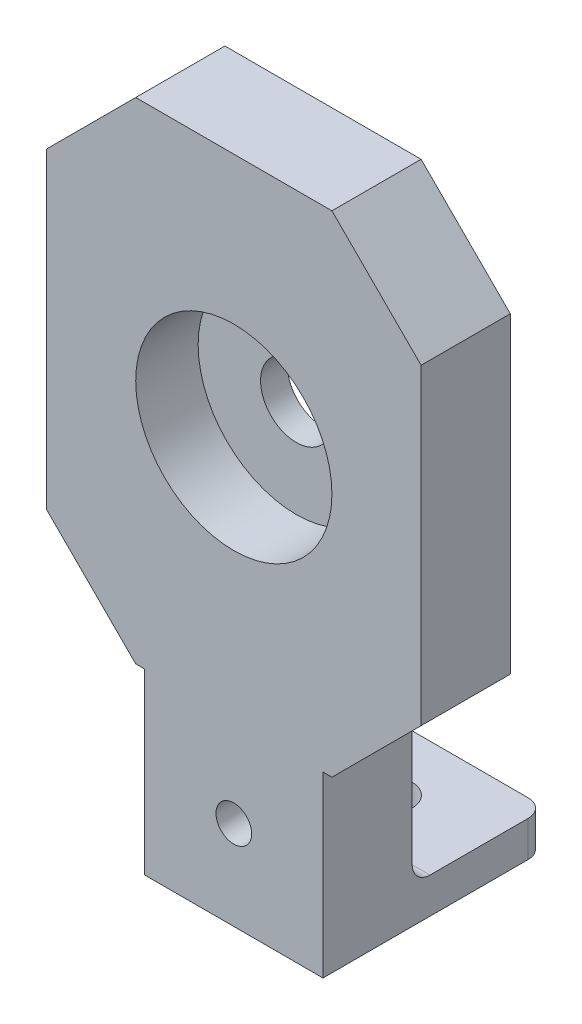
SolidWorks part; units mm, degrees
material "PLA"
ref_plane "Piano frontale" through (0, 0, 0) normal (0, 0, 1) x (1, 0, 0)
ref_plane "Piano superiore" through (0, 0, 0) normal (0, 1, 0) x (1, 0, 0)
ref_plane "Piano destro" through (0, 0, 0) normal (1, 0, 0) x (0, 0, -1)
sketch "Schizzo1" plane through (0, 0, 0) normal (0, 0, 1) x (1, 0, 0)
  line L0 (0, 0) -> (0, -47.5) construction
  line L1 (-10, -47.5) -> (10, -47.5)
  line L2 (-21, -27.5) -> (-21, 27.5)
  line L3 (-21, 27.5) -> (21, 27.5)
  line L4 (21, -27.5) -> (21, 27.5)
  line L5 (-21, -27.5) -> (21, 27.5) construction
  line L6 (-21, 27.5) -> (21, -27.5) construction
  line L7 (-10, -47.5) -> (-10, -27.5)
  line L8 (-10, -27.5) -> (-21, -27.5)
  line L9 (10, -47.5) -> (10, -27.5)
  line L10 (10, -27.5) -> (21, -27.5)
  point P0 (0, 0)
  dimension "D1" = 42
  dimension "D3" = 20
  dimension "D4" = 10
  dimension "D5" = 55
extrude "Estrusione-Estrusione1" add sketch "Schizzo1" along normal blind 10
sketch "Schizzo6" plane through (0, 0, 10) normal (0, 0, 1) x (1, 0, 0)
  line L0 (-10, -47.5) -> (10, -47.5) construction
  line L1 (21, 27.5) -> (-21, 27.5) construction
  circle A0 centre (0, 0) radius 11
  dimension "D1" = 22
  dimension "D2" = 47.5
extrude "Taglio-Estrusione4" cut sketch "Schizzo6" against normal blind 7
sketch "Schizzo7" plane through (0, 0, 3) normal (0, 0, 1) x (1, 0, 0)
  circle A0 centre (0, 0) radius 4
  dimension "D1" = 8
extrude "Taglio-Estrusione5" cut sketch "Schizzo7" against normal through all
chamfer "Smusso2" distance 10 angle 45 4 edges at (-21, -27.5, 5) (21, -27.5, 5) (21, 27.5, 5) (-21, 27.5, 5)
sketch "Schizzo8" plane through (0, 0, 0) normal (0, 0, -1) x (-1, 0, 0)
  line L0 (10, -27.5) -> (10, -47.5) construction
  line L1 (-10, -47.5) -> (10, -47.5)
  line L2 (-10, -47.5) -> (-10, -43.5)
  line L3 (-10, -43.5) -> (10, -43.5)
  line L4 (10, -47.5) -> (10, -43.5)
  dimension "D1" = 4
extrude "Estrusione-Estrusione3" add sketch "Schizzo8" along normal blind 15
sketch "Schizzo9" plane through (0, -43.5, 0) normal (0, 1, 0) x (1, 0, 0)
  line L0 (0, 15) -> (0, 0) construction
  line L1 (-10, 15) -> (10, 15) construction
  line L2 (11, 0) -> (-11, 0) construction
  circle A0 centre (0, 7.5) radius 2.5
  dimension "D1" = 5
  dimension "D3" = 7.5
extrude "Taglio-Estrusione6" cut sketch "Schizzo9" against normal blind 35
fillet "Raccordo1" radius 2 3 edges at (0, -43.5, 0) (-10, -45.5, -15) (10, -45.5, -15)
sketch "Schizzo10" plane through (0, 0, 0) normal (0, 0, -1) x (-1, 0, 0)
  line L0 (-8, -47.5) -> (8, -47.5) construction
  circle A0 centre (0, -37.5) radius 2
  dimension "D2" = 4
  dimension "D1" = 10
extrude "Taglio-Estrusione7" cut sketch "Schizzo10" against normal blind 10
